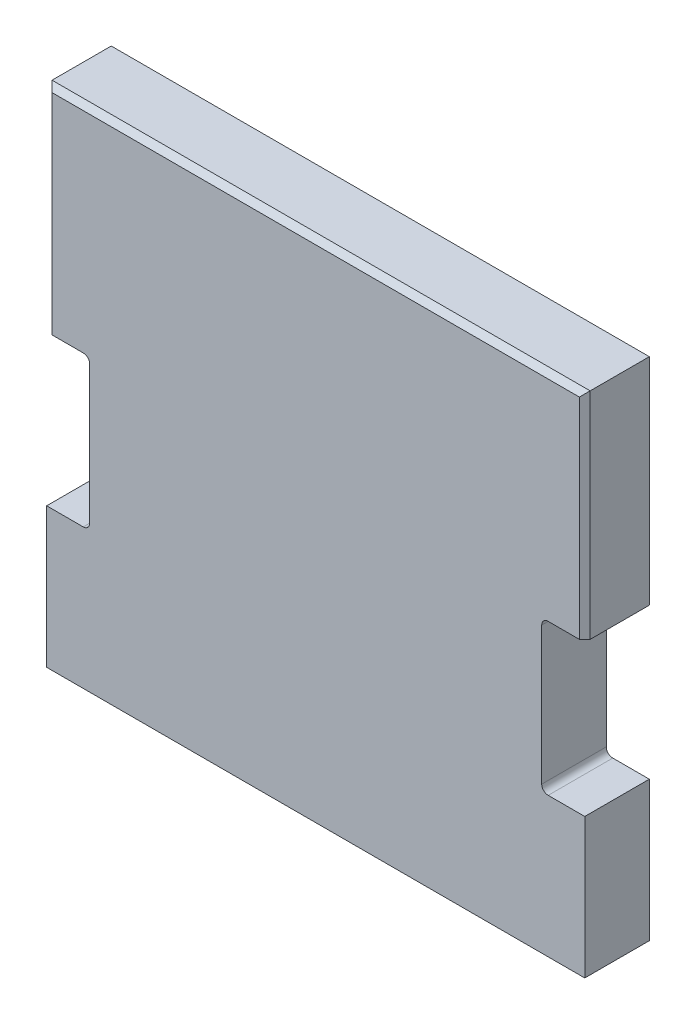
SolidWorks part; units mm, degrees
material "Стекло"
ref_plane "Front" through (0, 0, 0) normal (0, 0, 1) x (1, 0, 0)
ref_plane "Top" through (0, 0, 0) normal (0, 1, 0) x (1, 0, 0)
ref_plane "Right" through (0, 0, 0) normal (1, 0, 0) x (0, 0, -1)
sketch "Эскиз1" plane through (0, 0, 0) normal (0, 0, 1) x (1, 0, 0)
  line L0 (0, 0) -> (0, 6.5)
  line L1 (0, 6.5) -> (1.7, 6.5)
  line L2 (2, 6.8) -> (2, 13.2)
  line L3 (1.7, 13.5) -> (0, 13.5)
  line L4 (0, 13.5) -> (0, 23.5)
  line L5 (0, 23.5) -> (25, 23.5)
  line L6 (25, 23.5) -> (25, 13.5)
  line L7 (25, 13.5) -> (23.3, 13.5)
  line L8 (23, 13.2) -> (23, 6.8)
  line L9 (23.3, 6.5) -> (25, 6.5)
  line L10 (25, 6.5) -> (25, 0)
  line L11 (25, 0) -> (0, 0)
  arc A0 (23.3, 6.5) -> (23, 6.8) centre (23.3, 6.8) cw
  arc A1 (23, 13.2) -> (23.3, 13.5) centre (23.3, 13.2) cw
  arc A2 (1.7, 6.5) -> (2, 6.8) centre (1.7, 6.8) ccw
  arc A3 (2, 13.2) -> (1.7, 13.5) centre (1.7, 13.2) ccw
  dimension "D6" = 0.3
  dimension "D1" = 23.5
  dimension "D2" = 25
  dimension "D3" = 21
  dimension "D4" = 6.5
  dimension "D5" = 7
extrude "Бобышка-Вытянуть1" add sketch "Эскиз1" along normal blind 3
chamfer "Фаска1" distance 0.25 angle 45 3 edges at (25, 18.5, 3) (12.5, 23.5, 3) (0, 18.5, 3)
